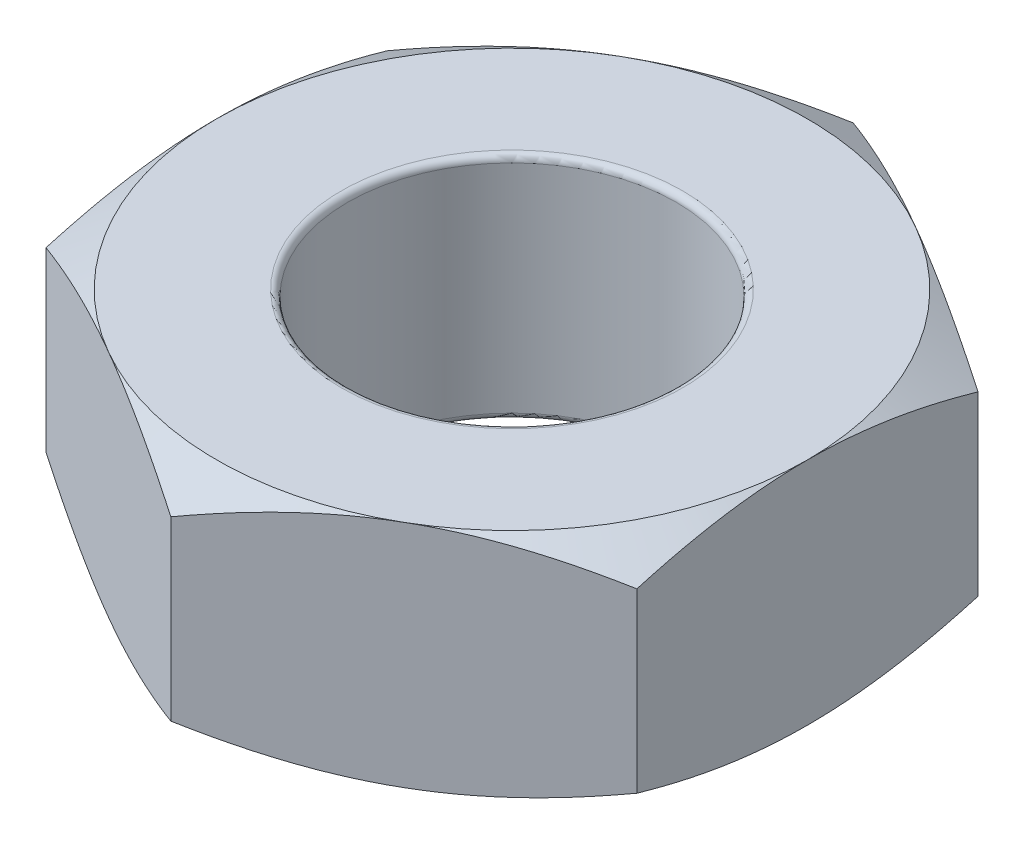
SolidWorks part; units mm, degrees
ref_plane "Front Plane" through (0, 0, 0) normal (0, 0, 1) x (1, 0, 0)
ref_plane "Top Plane" through (0, 0, 0) normal (0, 1, 0) x (1, 0, 0)
ref_plane "Right Plane" through (0, 0, 0) normal (1, 0, 0) x (0, 0, -1)
sketch "Sketch2" plane through (0, 0, 0) normal (0, 1, 0) x (1, 0, 0)
  line L1 (2.25, -1.299) -> (2.25, 1.299)
  line L2 (2.25, 1.299) -> (0, 2.5981)
  line L3 (0, 2.5981) -> (-2.25, 1.299)
  line L4 (-2.25, 1.299) -> (-2.25, -1.299)
  line L5 (-2.25, -1.299) -> (0, -2.5981)
  line L6 (0, -2.5981) -> (2.25, -1.299)
  circle A0 centre (0, 0) radius 1.25
  circle A1 centre (0, 0) radius 2.25 construction
  dimension "D1" = 2.5
  dimension "D2" = 4.5
extrude "Boss-Extrude1" add sketch "Sketch2" along normal blind 1.75
sketch "Sketch3" plane through (0, 1.75, 0) normal (0, 1, 0) x (1, 0, 0)
  circle A0 centre (0, 0) radius 2.25 construction
  circle A1 centre (0, 0) radius 2.25
extrude "Cut-Extrude1" cut sketch "Sketch3" against normal blind 2 draft 60 flip side to cut
sketch "Sketch4" plane through (0, 0, 0) normal (0, -1, 0) x (1, 0, 0)
  circle A0 centre (0, 0) radius 2.25 construction
  circle A1 centre (0, 0) radius 2.25
extrude "Cut-Extrude2" cut sketch "Sketch4" against normal blind 2 draft 60 flip side to cut
fillet "Fillet1" radius 0.05 2 edges at (0, 0, 1.25) (0, 1.75, 1.25)
